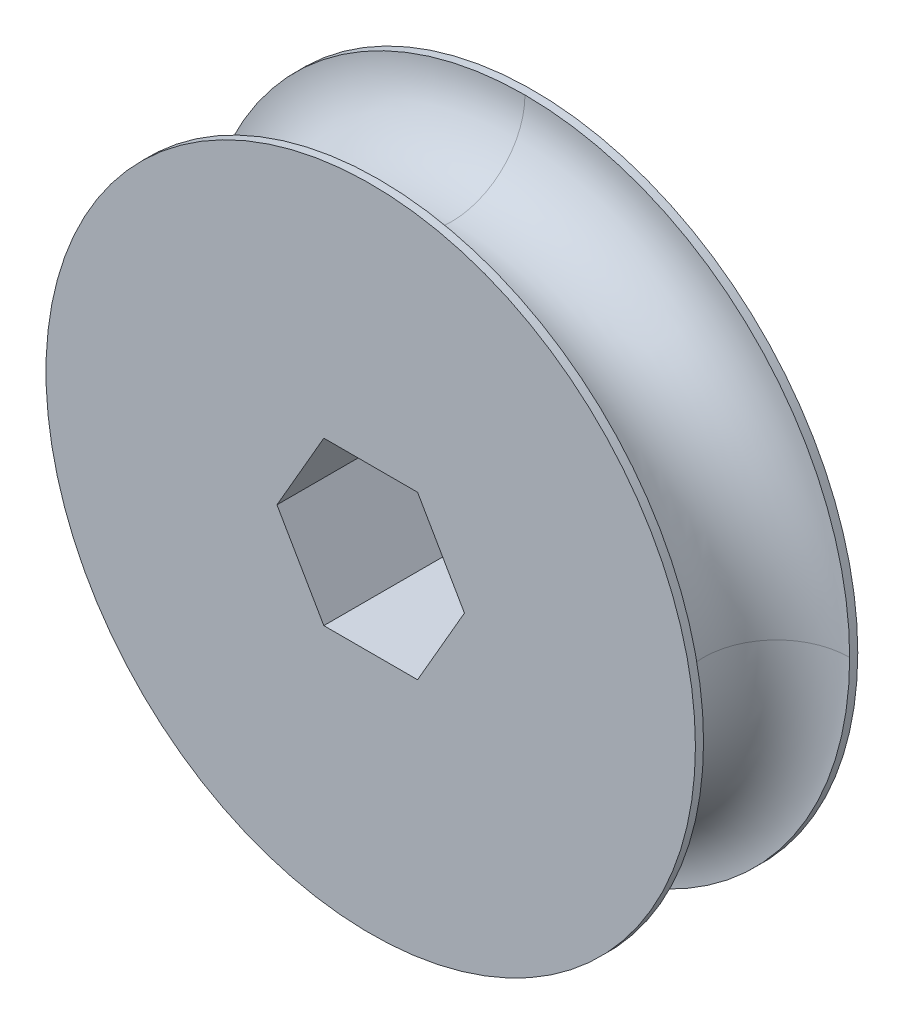
SolidWorks part; units mm, degrees
ref_plane "Front Plane" through (0, 0, 0) normal (0, 0, 1) x (1, 0, 0)
ref_plane "Top Plane" through (0, 0, 0) normal (0, 1, 0) x (1, 0, 0)
ref_plane "Right Plane" through (0, 0, 0) normal (1, 0, 0) x (0, 0, -1)
sketch "Sketch2" plane through (0, 0, 0) normal (0, 0, 1) x (1, 0, 0)
  circle A0 centre (0, 0) radius 25.4
extrude "Boss-Extrude2" add sketch "Sketch2" along normal blind 12.7
sketch "Sketch3" plane through (0, 0, 0) normal (1, 0, 0) x (0, 0, -1)
  line L0 (-12.065, 25.4) -> (-0.635, 25.4)
  arc A0 (-0.635, 25.4) -> (-12.065, 25.4) centre (-6.35, 25.4) cw
sweep "Cut-Sweep2" cut profiles "Sketch3" path edge at (25.4, 0, 12.7)
sketch "Sketch22" plane through (0, 0, 0) normal (0, 0, 1) x (1, 0, 0)
  line L1 (7.3323, 0) -> (3.6662, 6.35)
  line L2 (3.6662, 6.35) -> (-3.6662, 6.35)
  line L3 (-3.6662, 6.35) -> (-7.3323, 0)
  line L4 (-7.3323, 0) -> (-3.6662, -6.35)
  line L5 (-3.6662, -6.35) -> (3.6662, -6.35)
  line L6 (3.6662, -6.35) -> (7.3323, 0)
  circle A0 centre (0, 0) radius 6.35 construction
  dimension "D1" = 12.7
extrude "Cut-Extrude2" cut sketch "Sketch22" along normal blind 17.272
